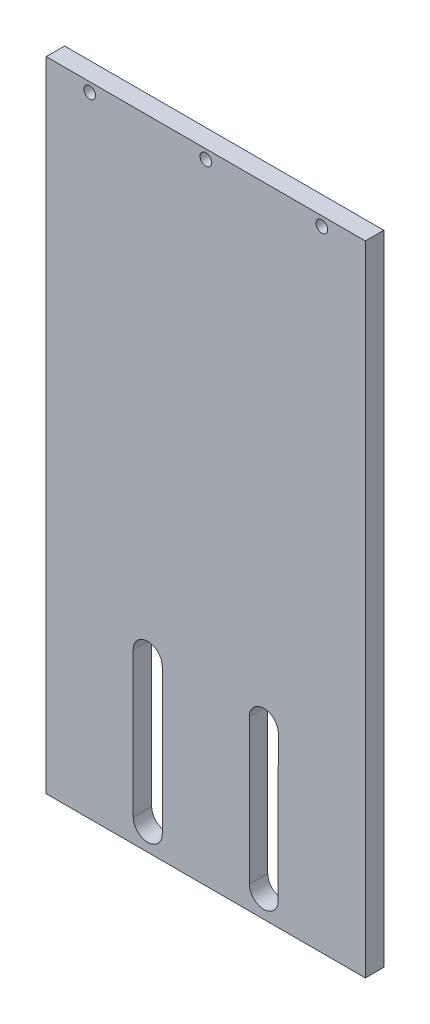
SolidWorks part; units mm, degrees
ref_plane "Alzado" through (0, 0, 0) normal (0, 0, 1) x (1, 0, 0)
ref_plane "Planta" through (0, 0, 0) normal (0, 1, 0) x (1, 0, 0)
ref_plane "Vista lateral" through (0, 0, 0) normal (1, 0, 0) x (0, 0, -1)
sketch "Croquis1" plane through (0, 0, 0) normal (0, 0, 1) x (1, 0, 0)
  line L1 (-55, -110) -> (55, -110)
  line L2 (-55, -110) -> (-55, 110)
  line L3 (-55, 110) -> (55, 110)
  line L4 (55, -110) -> (55, 110)
  line L5 (-55, -110) -> (55, 110) construction
  line L6 (-55, 110) -> (55, -110) construction
  point P0 (0, 0)
  dimension "D1" = 110
  dimension "D2" = 220
extrude "Saliente-Extruir1" add sketch "Croquis1" along normal blind 6.35
sketch "Croquis2" plane through (0, 0, 0) normal (0, 0, 1) x (1, 0, 0)
  line L0 (66.7052, 106.825) -> (-75.6472, 106.825) construction
  line L1 (55, 110) -> (-55, 110) construction
  line L2 (55, -110) -> (55, 110) construction
  line L3 (66.7052, -103.175) -> (-89.4456, -103.175) construction
  line L4 (-55, -110) -> (55, -110) construction
  line L5 (15, -52) -> (15, -102)
  line L6 (25, -52) -> (24.86, -103.175)
  line L7 (-25, -52) -> (-25, -102)
  line L8 (-15, -52) -> (-15, -102)
  line L9 (0, -110) -> (0, -44.6015) construction
  circle A0 centre (40, 106.825) radius 2
  circle A1 centre (-40, 106.825) radius 2
  circle A2 centre (0, 106.825) radius 2
  arc A4 (-15, -52) -> (-25, -52) centre (-20, -52) ccw
  arc A5 (-25, -102) -> (-15, -102) centre (-20, -102) ccw
  arc A6 (25, -52) -> (15, -52) centre (20, -52) ccw
  arc A7 (15, -102) -> (24.86, -103.175) centre (20, -102) ccw
  dimension "D2" = 4
  dimension "D3" = 4
  dimension "D9" = 10
  dimension "D10" = 10
  dimension "D11" = 20
  dimension "D12" = 50
  dimension "D13" = 50
  dimension "D14" = 4
  dimension "D1" = 3.175
  dimension "D4" = 80
  dimension "D5" = 15
  dimension "D6" = 210
  dimension "D7" = 8
  dimension "D8" = 8
  dimension "D15" = 20
extrude "Cortar-Extruir2" cut sketch "Croquis2" along normal through all
